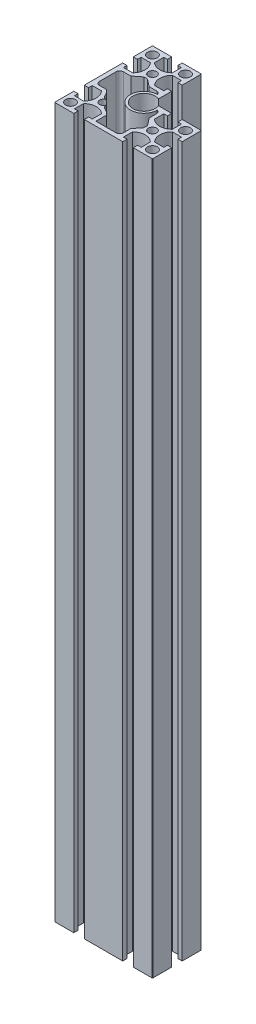
SolidWorks part; units mm, degrees
ref_plane "RefPlane1" through (0, 0, 0) normal (0, 0, 1) x (1, 0, 0)
ref_plane "RefPlane2" through (0, 0, 0) normal (0, 1, 0) x (1, 0, 0)
ref_plane "RefPlane3" through (0, 0, 0) normal (1, 0, 0) x (0, 0, -1)
sketch "草图2" plane through (0, 0, 0) normal (0, 1, 0) x (1, 0, 0)
  line L0 (201.4216, 152.0837) -> (212.33, 152.0837)
  line L1 (212.33, 148.5837) -> (212.33, 152.0837)
  line L2 (209.38, 148.5837) -> (212.33, 148.5837)
  line L3 (209.38, 141.0837) -> (209.38, 148.5837)
  line L4 (223.88, 148.5837) -> (223.88, 141.0837)
  line L5 (220.93, 148.5837) -> (223.88, 148.5837)
  line L6 (220.93, 152.0837) -> (220.93, 148.5837)
  line L7 (220.93, 152.0837) -> (236.13, 152.0837)
  line L8 (236.63, 151.5837) -> (236.63, 136.3837)
  line L9 (233.13, 136.3837) -> (236.63, 136.3837)
  line L10 (233.13, 139.3337) -> (233.13, 136.3837)
  line L11 (225.63, 139.3337) -> (233.13, 139.3337)
  line L12 (233.13, 124.8337) -> (225.63, 124.8337)
  line L13 (233.13, 127.7837) -> (233.13, 124.8337)
  line L14 (236.63, 127.7837) -> (233.13, 127.7837)
  line L15 (236.63, 127.7837) -> (236.63, 112.5837)
  line L16 (236.13, 112.0837) -> (220.93, 112.0837)
  line L17 (220.93, 115.5837) -> (220.93, 112.0837)
  line L18 (223.88, 115.5837) -> (220.93, 115.5837)
  line L19 (223.88, 123.0837) -> (223.88, 115.5837)
  line L20 (209.38, 115.5837) -> (209.38, 123.0837)
  line L21 (212.33, 115.5837) -> (209.38, 115.5837)
  line L22 (212.33, 112.0837) -> (212.33, 115.5837)
  line L23 (212.33, 112.0837) -> (196.13, 112.0837)
  line L24 (203.38, 115.5837) -> (186.88, 115.5837)
  line L25 (206.38, 124.5837) -> (206.38, 118.5837)
  line L26 (211.13, 130.5837) -> (206.38, 124.5837)
  line L27 (211.13, 133.5837) -> (211.13, 130.5837)
  line L28 (206.38, 139.5837) -> (211.13, 133.5837)
  line L29 (206.38, 145.5837) -> (206.38, 139.5837)
  line L30 (172.33, 188.5837) -> (172.33, 192.0837)
  line L31 (169.38, 188.5837) -> (172.33, 188.5837)
  line L32 (169.38, 181.0837) -> (169.38, 188.5837)
  line L33 (183.88, 188.5837) -> (183.88, 181.0837)
  line L34 (180.93, 188.5837) -> (183.88, 188.5837)
  line L35 (180.93, 192.0837) -> (180.93, 188.5837)
  line L36 (180.93, 192.0837) -> (196.13, 192.0837)
  line L37 (196.63, 191.5837) -> (196.63, 176.3837)
  line L38 (193.13, 176.3837) -> (196.63, 176.3837)
  line L39 (193.13, 179.3337) -> (193.13, 176.3837)
  line L40 (185.63, 179.3337) -> (193.13, 179.3337)
  line L41 (193.13, 164.8337) -> (185.63, 164.8337)
  line L42 (193.13, 167.7837) -> (193.13, 164.8337)
  line L43 (196.63, 167.7837) -> (193.13, 167.7837)
  line L44 (196.63, 167.7837) -> (196.63, 156.8753)
  line L45 (196.13, 112.0837) -> (180.93, 112.0837)
  line L46 (180.93, 115.5837) -> (180.93, 112.0837)
  line L47 (183.88, 115.5837) -> (180.93, 115.5837)
  line L48 (183.88, 123.0837) -> (183.88, 115.5837)
  line L49 (186.88, 124.2361) -> (186.88, 115.5837)
  line L50 (169.38, 115.5837) -> (169.38, 123.0837)
  line L51 (172.33, 115.5837) -> (169.38, 115.5837)
  line L52 (172.33, 112.0837) -> (172.33, 115.5837)
  line L53 (172.33, 112.0837) -> (157.13, 112.0837)
  line L54 (156.63, 112.5837) -> (156.63, 127.7837)
  line L55 (160.13, 127.7837) -> (156.63, 127.7837)
  line L56 (160.13, 124.8337) -> (160.13, 127.7837)
  line L57 (167.63, 124.8337) -> (160.13, 124.8337)
  line L58 (160.13, 139.3337) -> (167.63, 139.3337)
  line L59 (160.13, 136.3837) -> (160.13, 139.3337)
  line L60 (156.63, 136.3837) -> (160.13, 136.3837)
  line L61 (156.63, 136.3837) -> (156.63, 167.7837)
  line L62 (160.13, 167.7837) -> (156.63, 167.7837)
  line L63 (160.13, 164.8337) -> (160.13, 167.7837)
  line L64 (167.63, 164.8337) -> (160.13, 164.8337)
  line L65 (160.13, 176.3837) -> (160.13, 179.3337)
  line L66 (156.63, 176.3837) -> (160.13, 176.3837)
  line L67 (156.63, 176.3837) -> (156.63, 191.5837)
  line L68 (157.13, 192.0837) -> (172.33, 192.0837)
  line L69 (184.13, 161.8337) -> (190.13, 161.8337)
  line L70 (178.13, 166.5837) -> (184.13, 161.8337)
  line L71 (175.13, 166.5837) -> (178.13, 166.5837)
  line L72 (169.13, 161.8337) -> (175.13, 166.5837)
  line L73 (163.13, 161.8337) -> (169.13, 161.8337)
  line L74 (160.13, 145.3337) -> (160.13, 158.8337)
  line L75 (168.7825, 142.3337) -> (163.13, 142.3337)
  line L76 (160.13, 179.3337) -> (167.63, 179.3337)
  arc A0 (209.38, 141.0837) -> (223.88, 141.0837) centre (216.63, 148.3441) ccw
  arc A1 (236.63, 151.5837) -> (236.13, 152.0837) centre (236.13, 151.5837) ccw
  arc A2 (225.63, 139.3337) -> (225.63, 124.8337) centre (232.8904, 132.0837) ccw
  arc A3 (236.13, 112.0837) -> (236.63, 112.5837) centre (236.13, 112.5837) ccw
  arc A4 (223.88, 123.0837) -> (209.38, 123.0837) centre (216.63, 115.8233) ccw
  arc A5 (203.38, 115.5837) -> (206.38, 118.5837) centre (203.38, 118.5837) ccw
  arc A6 (206.38, 145.5837) -> (204.1296, 148.4885) centre (203.38, 145.5837) ccw
  circle A7 centre (230.63, 118.0837) radius 4
  circle A8 centre (230.13, 145.5837) radius 4
  circle A9 centre (216.63, 132.0837) radius 3.4
  arc A10 (169.38, 181.0837) -> (183.88, 181.0837) centre (176.63, 188.3441) ccw
  arc A11 (196.63, 191.5837) -> (196.13, 192.0837) centre (196.13, 191.5837) ccw
  arc A12 (185.63, 179.3337) -> (185.63, 164.8337) centre (192.8904, 172.0837) ccw
  arc A13 (183.88, 123.0837) -> (169.38, 123.0837) centre (176.63, 115.8233) ccw
  arc A14 (186.88, 124.2361) -> (181.5934, 128.1198) centre (176.63, 115.8233) ccw
  arc A15 (156.63, 112.5837) -> (157.13, 112.0837) centre (157.13, 112.5837) ccw
  arc A16 (167.63, 124.8337) -> (167.63, 139.3337) centre (160.3696, 132.0837) ccw
  arc A17 (172.6661, 137.0471) -> (168.7825, 142.3337) centre (160.3696, 132.0837) ccw
  arc A18 (167.63, 164.8337) -> (167.63, 179.3337) centre (160.3696, 172.0837) ccw
  arc A19 (157.13, 192.0837) -> (156.63, 191.5837) centre (157.13, 191.5837) ccw
  arc A20 (193.0349, 159.5833) -> (190.13, 161.8337) centre (190.13, 158.8337) ccw
  arc A21 (163.13, 161.8337) -> (160.13, 158.8337) centre (163.13, 158.8337) ccw
  arc A22 (160.13, 145.3337) -> (163.13, 142.3337) centre (163.13, 145.3337) ccw
  circle A23 centre (176.63, 172.0837) radius 3.4
  circle A24 centre (190.13, 185.5837) radius 4
  circle A25 centre (162.63, 118.0837) radius 4
  circle A26 centre (163.13, 186.0837) radius 4
  circle A27 centre (176.63, 132.0837) radius 3.2
  arc A28 (179.7713, 131.4736) -> (181.5934, 128.1198) centre (182.7163, 130.9017) ccw
  arc A29 (172.6661, 137.0471) -> (176.02, 135.225) centre (175.448, 138.17) ccw
  arc A30 (196.63, 156.8753) -> (201.4216, 152.0837) centre (193.13, 148.5837) ccw
  arc A31 (193.0349, 159.5833) -> (204.1296, 148.4885) centre (193.13, 148.5837) ccw
  dimension "D1" = 6
  dimension "D2" = 6
  dimension "D3" = 6
  dimension "D4" = 6.5
  dimension "D5" = 6.5
  dimension "D6" = 6
  dimension "D7" = 6
extrude "凸台-拉伸1" add sketch "草图2" along normal blind 580 contours A30 L44 L43 L42 L41 A12 L40 L39 L38 L37 A11 L36 L35 L34 L33 A10 L32 L31 L30 L68 A19 L67 L66 L65 L76 A18 L64 L63 L62 L61 L60 L59 L58 A16 L57 L56 L55 L54 A15 L53 L52 L51 L50 A13 L48 L47 L46 L45 L23 L22 L21
sketch "草图3" plane through (0, 580, 0) normal (0, 1, 0) x (1, 0, 0)
  circle A0 centre (163.13, 186.0837) radius 5.3414
  circle A1 centre (190.13, 185.5837) radius 5.3835
  circle A2 centre (162.63, 118.0837) radius 4.9338
  circle A3 centre (230.63, 118.0837) radius 5.418
  circle A4 centre (230.13, 145.5837) radius 5.5743
extrude "凸台-拉伸2" add sketch "草图3" against normal up to surface (580 mm away) up to face at (230.63, 0, -114.0837)
sketch "草图4" plane through (0, 580, 0) normal (0, 1, 0) x (1, 0, 0)
  line L0 (216.63, 132.0837) -> (248.5113, 132.0837) construction
  line L1 (176.63, 172.0837) -> (176.63, 201.502) construction
  line L2 (156.63, 152.0837) -> (248.5113, 152.0837) construction
  line L3 (156.63, 136.3837) -> (156.63, 167.7837) construction
  line L5 (196.63, 112.0837) -> (196.63, 167.7837) construction
  line L6 (212.33, 112.0837) -> (180.93, 112.0837) construction
  circle A0 centre (163.13, 185.5837) radius 4
  circle A1 centre (163.13, 118.5837) radius 4
  circle A2 centre (230.13, 118.5837) radius 4
  circle A3 centre (230.13, 145.5837) radius 4
  circle A4 centre (190.13, 185.5837) radius 4
  dimension "D1" = 8
  dimension "D2" = 8
  dimension "D3" = 8
  dimension "D4" = 8
  dimension "D5" = 8
  dimension "D6" = 27
  dimension "D7" = 27
  dimension "D8" = 67
  dimension "D9" = 13.5
  dimension "D10" = 67
  dimension "D11" = 33.5
extrude "切除-拉伸1" cut sketch "草图4" against normal through all
